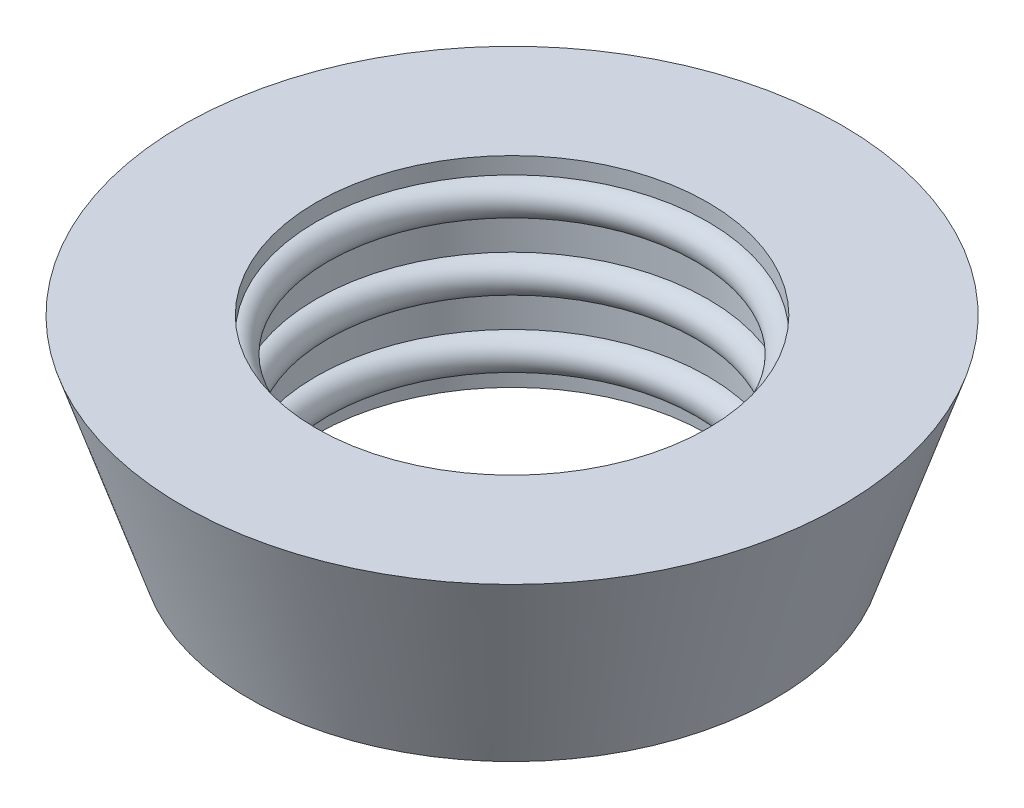
SolidWorks part; units mm, degrees
material "201 Annealed Stainless Steel (SS)"
ref_plane "Front Plane" through (0, 0, 0) normal (0, 0, 1) x (1, 0, 0)
ref_plane "Top Plane" through (0, 0, 0) normal (0, 1, 0) x (1, 0, 0)
ref_plane "Right Plane" through (0, 0, 0) normal (1, 0, 0) x (0, 0, -1)
sketch "Sketch1" plane through (0, 0, 0) normal (0, 0, 1) x (1, 0, 0)
  line L0 (0, 0) -> (0, 75.0492) construction
  line L1 (5.85, 0) -> (7.85, 0)
  line L2 (7.85, 0) -> (9.85, 6)
  line L3 (9.85, 6) -> (5.85, 6)
  line L4 (5.85, 6) -> (5.85, 5.5)
  line L5 (5.85, 2.5) -> (5.85, 1.5)
  line L6 (5.85, 4.5) -> (5.85, 3.5)
  line L7 (5.85, 0.5) -> (5.85, 0)
  arc A0 (5.85, 1.5) -> (5.85, 0.5) centre (5.85, 1) ccw
  arc A1 (5.85, 3.5) -> (5.85, 2.5) centre (5.85, 3) ccw
  arc A2 (5.85, 5.5) -> (5.85, 4.5) centre (5.85, 5) ccw
  point P13 (0, 0)
  point P14 (0, 0)
  dimension "D5" = 1
  dimension "D1" = 5.85
  dimension "D2" = 2
  dimension "D3" = 4
  dimension "D4" = 6
  dimension "D6" = 2
  dimension "D7" = 2
  dimension "D8" = 1
revolve "Revolve1" add sketch "Sketch1" angle 360 about L0
equation "\"D1@Sketch1\"=11.7/2"
